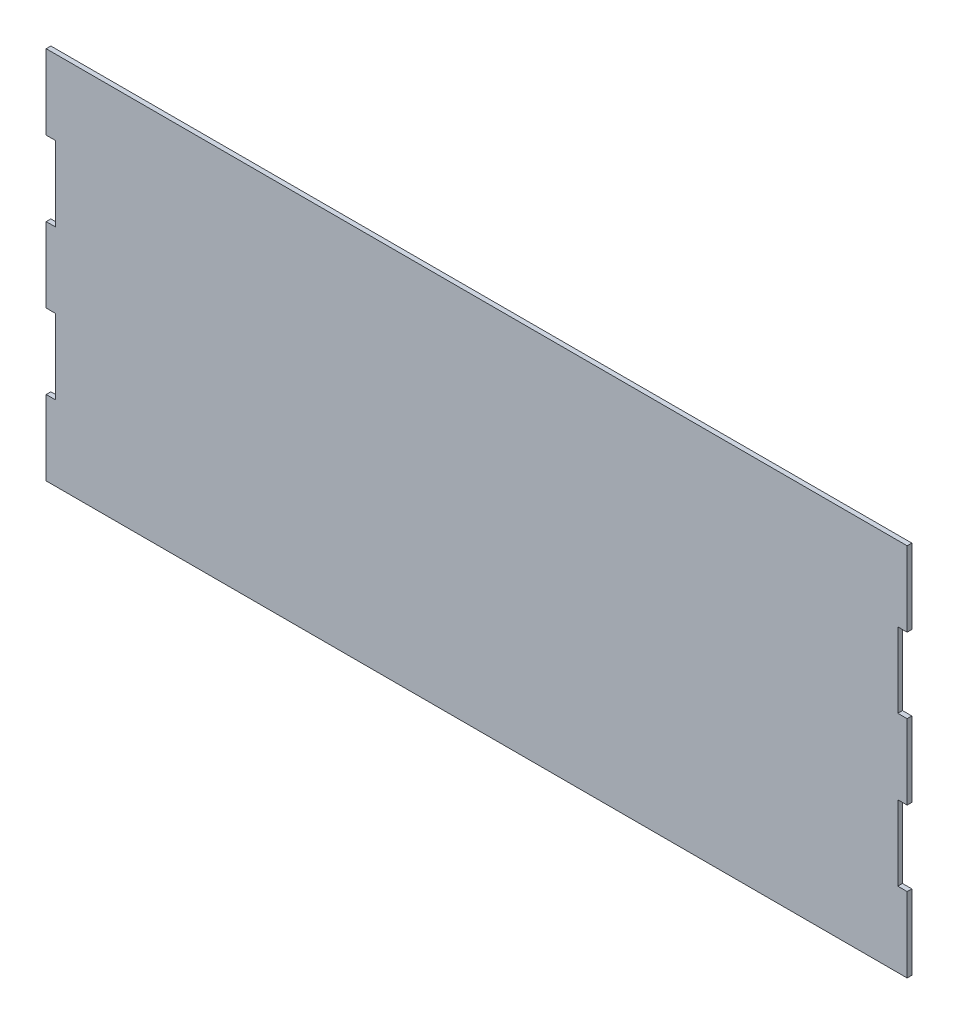
SolidWorks part; units mm, degrees
ref_plane "Front Plane" through (0, 0, 0) normal (0, 0, 1) x (1, 0, 0)
ref_plane "Top Plane" through (0, 0, 0) normal (0, 1, 0) x (1, 0, 0)
ref_plane "Right Plane" through (0, 0, 0) normal (1, 0, 0) x (0, 0, -1)
sketch "Sketch1" plane through (0, 0, 0) normal (0, 0, 1) x (1, 0, 0)
  line L0 (0, 203.2) -> (6.35, 203.2)
  line L1 (0, 0) -> (584.2, 0)
  line L2 (0, 0) -> (0, 50.8)
  line L3 (0, 254) -> (584.2, 254)
  line L4 (584.2, 0) -> (584.2, 50.8)
  line L5 (6.35, 203.2) -> (6.35, 152.4)
  line L6 (6.35, 152.4) -> (0, 152.4)
  line L7 (0, 101.6) -> (6.35, 101.6)
  line L8 (6.35, 101.6) -> (6.35, 50.8)
  line L9 (6.35, 50.8) -> (0, 50.8)
  line L10 (0, 0) -> (6.35, 0)
  line L11 (6.35, 0) -> (6.35, -50.8)
  line L12 (6.35, -50.8) -> (0, -50.8)
  line L13 (0, 101.6) -> (0, 152.4)
  line L14 (0, 203.2) -> (0, 254)
  line L15 (292.1, 254) -> (292.1, 0) construction
  line L16 (577.85, 50.8) -> (584.2, 50.8)
  line L17 (577.85, 101.6) -> (577.85, 50.8)
  line L18 (584.2, 101.6) -> (577.85, 101.6)
  line L19 (577.85, 152.4) -> (584.2, 152.4)
  line L20 (577.85, 203.2) -> (577.85, 152.4)
  line L21 (584.2, 203.2) -> (577.85, 203.2)
  line L22 (584.2, 203.2) -> (584.2, 254)
  line L23 (584.2, 101.6) -> (584.2, 152.4)
  line L24 (25.4, 254) -> (25.4, 0) construction
  line L25 (558.8, 254) -> (558.8, 0) construction
  dimension "D1" = 254
  dimension "D2" = 584.2
  dimension "D3" = 6.35
  dimension "D4" = 50.8
  dimension "D5" = 50.8
  dimension "D7" = 25.4
  dimension "D8" = 25.4
  dimension "D6" = 3
extrude "Boss-Extrude1" add sketch "Sketch1" along normal blind 3.175 contours L18 L23 L19 L20 L21 L22 L3 L14 L0 L5 L6 L13 L7 L8 L9 L2 L1 L4 L16 L17
sketch "Sketch4" plane through (0, 0, 3.175) normal (0, 0, 1) x (1, 0, 0)
  line L1 (312.1555, -0.0167) -> (312.1555, 59.8139)
  line L2 (312.1555, 74.3399) -> (312.1555, 179.5864)
  line L3 (312.1555, 194.1124) -> (312.1555, 254)
  line L4 (308.524, 134.2248) -> (308.524, 239.474)
  line L5 (308.524, 14.4495) -> (308.524, 119.6988)
  line L6 (565.15, 194.1124) -> (565.15, 254)
  line L7 (65.2135, -0.0167) -> (57.9505, -0.0167)
  line L8 (312.1555, -0.0167) -> (319.4185, -0.0167)
  line L9 (312.1555, 254) -> (319.4185, 254)
  line L10 (57.9505, -0.0167) -> (45.8455, -0.0167)
  line L11 (65.2135, 254) -> (57.9505, 254)
  line L12 (57.9505, 254) -> (45.8455, 254)
  line L13 (68.845, 134.2248) -> (68.845, 239.474)
  line L14 (54.319, 134.2248) -> (54.319, 239.474)
  line L15 (61.582, 134.2248) -> (61.582, 239.474)
  line L16 (57.9505, 74.3399) -> (57.9505, 179.5864)
  line L17 (61.582, 14.4495) -> (61.582, 119.6988)
  line L18 (65.2135, 194.1124) -> (65.2135, 254)
  line L19 (70.948, 14.4495) -> (70.948, 119.6988)
  line L20 (57.9505, 194.1124) -> (57.9505, 254)
  line L21 (54.319, 14.4495) -> (54.319, 119.6988)
  line L22 (65.2135, 74.3399) -> (65.2135, 179.5864)
  line L23 (65.2135, -0.0167) -> (65.2135, 59.8139)
  line L24 (57.9505, -0.0167) -> (57.9505, 59.8139)
  line L25 (72.4765, -0.0167) -> (65.2135, -0.0167)
  line L26 (79.7395, 254) -> (72.4765, 254)
  line L27 (72.4765, 254) -> (65.2135, 254)
  line L28 (79.7395, -0.0167) -> (72.4765, -0.0167)
  line L29 (94.2655, 254) -> (87.0025, 254)
  line L30 (87.0025, 254) -> (79.7395, 254)
  line L31 (94.2655, -0.0167) -> (87.0025, -0.0167)
  line L32 (87.0025, -0.0167) -> (79.7395, -0.0167)
  line L33 (76.108, 134.2248) -> (76.108, 239.474)
  line L34 (90.634, 14.4495) -> (90.634, 119.6988)
  line L35 (94.2655, 194.1124) -> (94.2655, 254)
  line L36 (97.897, 134.2248) -> (97.897, 239.474)
  line L37 (72.4765, -0.0167) -> (72.4765, 59.8139)
  line L38 (79.7395, 194.1124) -> (79.7395, 254)
  line L39 (72.4765, 74.3399) -> (72.4765, 179.5864)
  line L40 (90.634, 134.2248) -> (90.634, 239.474)
  line L41 (94.2655, 74.3399) -> (94.2655, 179.5864)
  line L42 (79.7395, 74.3399) -> (79.7395, 179.5864)
  line L43 (87.0025, 74.3399) -> (87.0025, 179.5864)
  line L44 (97.897, 14.4495) -> (97.897, 119.6988)
  line L45 (83.371, 134.2248) -> (83.371, 239.474)
  line L46 (72.4765, 194.1124) -> (72.4765, 254)
  line L47 (76.108, 14.4495) -> (76.108, 119.6988)
  line L48 (79.7395, -0.0167) -> (79.7395, 59.8139)
  line L49 (83.371, 14.4495) -> (83.371, 119.6988)
  line L50 (87.0025, 194.1124) -> (87.0025, 254)
  line L51 (94.2655, -0.0167) -> (94.2655, 59.8139)
  line L52 (87.0025, -0.0167) -> (87.0025, 59.8139)
  line L53 (101.5285, 254) -> (94.2655, 254)
  line L54 (108.7915, -0.0167) -> (101.5285, -0.0167)
  line L55 (101.5285, -0.0167) -> (94.2655, -0.0167)
  line L56 (108.7915, 254) -> (101.5285, 254)
  line L57 (123.3175, -0.0167) -> (116.0545, -0.0167)
  line L58 (116.0545, -0.0167) -> (108.7915, -0.0167)
  line L59 (123.3175, 254) -> (116.0545, 254)
  line L60 (116.0545, 254) -> (108.7915, 254)
  line L61 (119.686, 134.2248) -> (119.686, 239.474)
  line L62 (101.5285, -0.0167) -> (101.5285, 59.8139)
  line L63 (101.5285, 194.1124) -> (101.5285, 254)
  line L64 (108.7915, -0.0167) -> (108.7915, 59.8139)
  line L65 (105.16, 14.4495) -> (105.16, 119.6988)
  line L66 (108.7915, 194.1124) -> (108.7915, 254)
  line L67 (123.3175, 194.1124) -> (123.3175, 254)
  line L68 (101.5285, 74.3399) -> (101.5285, 179.5864)
  line L69 (123.3175, 74.3399) -> (123.3175, 179.5864)
  line L70 (126.949, 14.4495) -> (126.949, 119.6988)
  line L71 (108.7915, 74.3399) -> (108.7915, 179.5864)
  line L72 (126.949, 134.2248) -> (126.949, 239.474)
  line L73 (112.423, 134.2248) -> (112.423, 239.474)
  line L74 (112.423, 14.4495) -> (112.423, 119.6988)
  line L75 (116.0545, 74.3399) -> (116.0545, 179.5864)
  line L76 (116.0545, 194.1124) -> (116.0545, 254)
  line L77 (105.16, 134.2248) -> (105.16, 239.474)
  line L78 (119.686, 14.4495) -> (119.686, 119.6988)
  line L80 (123.3175, -0.0167) -> (123.3175, 59.8139)
  line L81 (116.0545, -0.0167) -> (116.0545, 59.8139)
  line L83 (130.5805, -0.0167) -> (123.3175, -0.0167)
  line L85 (137.8435, -0.0167) -> (130.5805, -0.0167)
  line L86 (137.8435, 254) -> (130.5805, 254)
  line L87 (130.5805, 254) -> (123.3175, 254)
  line L88 (152.3695, -0.0167) -> (145.1065, -0.0167)
  line L89 (145.1065, -0.0167) -> (137.8435, -0.0167)
  line L90 (152.3695, 254) -> (145.1065, 254)
  line L91 (145.1065, 254) -> (137.8435, 254)
  line L92 (156.001, 134.2248) -> (156.001, 239.474)
  line L93 (137.8435, 194.1124) -> (137.8435, 254)
  line L94 (134.212, 134.2248) -> (134.212, 239.474)
  line L95 (130.5805, 194.1124) -> (130.5805, 254)
  line L96 (130.5805, -0.0167) -> (130.5805, 59.8139)
  line L97 (137.8435, 74.3399) -> (137.8435, 179.5864)
  line L98 (130.5805, 74.3399) -> (130.5805, 179.5864)
  line L99 (156.001, 14.4495) -> (156.001, 119.6988)
  line L100 (148.738, 134.2248) -> (148.738, 239.474)
  line L101 (141.475, 134.2248) -> (141.475, 239.474)
  line L102 (152.3695, 74.3399) -> (152.3695, 179.5864)
  line L103 (152.3695, 194.1124) -> (152.3695, 254)
  line L104 (148.738, 14.4495) -> (148.738, 119.6988)
  line L105 (137.8435, -0.0167) -> (137.8435, 59.8139)
  line L106 (145.1065, 74.3399) -> (145.1065, 179.5864)
  line L107 (145.1065, 194.1124) -> (145.1065, 254)
  line L108 (134.212, 14.4495) -> (134.212, 119.6988)
  line L109 (141.475, 14.4495) -> (141.475, 119.6988)
  line L110 (152.3695, -0.0167) -> (152.3695, 59.8139)
  line L111 (145.1065, -0.0167) -> (145.1065, 59.8139)
  line L112 (159.6325, -0.0167) -> (152.3695, -0.0167)
  line L113 (174.1585, 254) -> (166.8955, 254)
  line L114 (166.8955, -0.0167) -> (159.6325, -0.0167)
  line L115 (181.4215, 254) -> (174.1585, 254)
  line L116 (166.8955, 254) -> (159.6325, 254)
  line L117 (159.6325, 254) -> (152.3695, 254)
  line L118 (181.4215, -0.0167) -> (174.1585, -0.0167)
  line L119 (174.1585, -0.0167) -> (166.8955, -0.0167)
  line L120 (163.264, 14.4495) -> (163.264, 119.6988)
  line L121 (166.8955, 74.3399) -> (166.8955, 179.5864)
  line L122 (170.527, 14.4495) -> (170.527, 119.6988)
  line L123 (159.6325, 74.3399) -> (159.6325, 179.5864)
  line L124 (185.053, 134.2248) -> (185.053, 239.474)
  line L125 (174.1585, 194.1124) -> (174.1585, 254)
  line L126 (174.1585, 74.3399) -> (174.1585, 179.5864)
  line L127 (185.053, 14.4495) -> (185.053, 119.6988)
  line L128 (177.79, 134.2248) -> (177.79, 239.474)
  line L129 (170.527, 134.2248) -> (170.527, 239.474)
  line L130 (181.4215, 194.1124) -> (181.4215, 254)
  line L131 (159.6325, -0.0167) -> (159.6325, 59.8139)
  line L132 (166.8955, 194.1124) -> (166.8955, 254)
  line L133 (181.4215, 74.3399) -> (181.4215, 179.5864)
  line L134 (177.79, 14.4495) -> (177.79, 119.6988)
  line L135 (159.6325, 194.1124) -> (159.6325, 254)
  line L136 (163.264, 134.2248) -> (163.264, 239.474)
  line L137 (166.8955, -0.0167) -> (166.8955, 59.8139)
  line L138 (181.4215, -0.0167) -> (181.4215, 59.8139)
  line L139 (174.1585, -0.0167) -> (174.1585, 59.8139)
  line L140 (188.6845, 254) -> (181.4215, 254)
  line L141 (203.2105, 254) -> (195.9475, 254)
  line L142 (195.9475, 254) -> (188.6845, 254)
  line L143 (195.9475, -0.0167) -> (188.6845, -0.0167)
  line L144 (188.6845, -0.0167) -> (181.4215, -0.0167)
  line L145 (210.4735, 254) -> (203.2105, 254)
  line L146 (210.4735, -0.0167) -> (203.2105, -0.0167)
  line L147 (203.2105, -0.0167) -> (195.9475, -0.0167)
  line L148 (195.9475, -0.0167) -> (195.9475, 59.8139)
  line L149 (210.4735, 74.3399) -> (210.4735, 179.5864)
  line L150 (195.9475, 74.3399) -> (195.9475, 179.5864)
  line L151 (203.2105, 194.1124) -> (203.2105, 254)
  line L152 (199.579, 134.2248) -> (199.579, 239.474)
  line L153 (203.2105, 74.3399) -> (203.2105, 179.5864)
  line L154 (192.316, 134.2248) -> (192.316, 239.474)
  line L155 (188.6845, -0.0167) -> (188.6845, 59.8139)
  line L156 (199.579, 14.4495) -> (199.579, 119.6988)
  line L157 (206.842, 14.4495) -> (206.842, 119.6988)
  line L158 (188.6845, 194.1124) -> (188.6845, 254)
  line L159 (214.105, 14.4495) -> (214.105, 119.6988)
  line L160 (195.9475, 194.1124) -> (195.9475, 254)
  line L161 (188.6845, 74.3399) -> (188.6845, 179.5864)
  line L162 (192.316, 14.4495) -> (192.316, 119.6988)
  line L163 (210.4735, 194.1124) -> (210.4735, 254)
  line L164 (214.105, 134.2248) -> (214.105, 239.474)
  line L165 (206.842, 134.2248) -> (206.842, 239.474)
  line L166 (210.4735, -0.0167) -> (210.4735, 59.8139)
  line L167 (203.2105, -0.0167) -> (203.2105, 59.8139)
  line L168 (224.9995, 254) -> (217.7365, 254)
  line L169 (217.7365, 254) -> (210.4735, 254)
  line L170 (224.9995, -0.0167) -> (217.7365, -0.0167)
  line L171 (217.7365, -0.0167) -> (210.4735, -0.0167)
  line L172 (232.2625, 254) -> (224.9995, 254)
  line L173 (239.5255, -0.0167) -> (232.2625, -0.0167)
  line L174 (232.2625, -0.0167) -> (224.9995, -0.0167)
  line L175 (239.5255, 254) -> (232.2625, 254)
  line L176 (224.9995, 194.1124) -> (224.9995, 254)
  line L177 (217.7365, 194.1124) -> (217.7365, 254)
  line L178 (217.7365, 74.3399) -> (217.7365, 179.5864)
  line L179 (228.631, 134.2248) -> (228.631, 239.474)
  line L180 (235.894, 134.2248) -> (235.894, 239.474)
  line L181 (239.5255, 74.3399) -> (239.5255, 179.5864)
  line L182 (224.9995, 74.3399) -> (224.9995, 179.5864)
  line L183 (232.2625, 194.1124) -> (232.2625, 254)
  line L184 (243.157, 134.2248) -> (243.157, 239.474)
  line L185 (224.9995, -0.0167) -> (224.9995, 59.8139)
  line L186 (239.5255, 194.1124) -> (239.5255, 254)
  line L187 (228.631, 14.4495) -> (228.631, 119.6988)
  line L188 (221.368, 134.2248) -> (221.368, 239.474)
  line L189 (235.894, 14.4495) -> (235.894, 119.6988)
  line L190 (243.157, 14.4495) -> (243.157, 119.6988)
  line L191 (232.2625, 74.3399) -> (232.2625, 179.5864)
  line L192 (217.7365, -0.0167) -> (217.7365, 59.8139)
  line L193 (221.368, 14.4495) -> (221.368, 119.6988)
  line L194 (239.5255, -0.0167) -> (239.5255, 59.8139)
  line L195 (232.2625, -0.0167) -> (232.2625, 59.8139)
  line L196 (261.3145, 254) -> (254.0515, 254)
  line L197 (254.0515, -0.0167) -> (246.7885, -0.0167)
  line L198 (246.7885, -0.0167) -> (239.5255, -0.0167)
  line L199 (268.5775, 254) -> (261.3145, 254)
  line L200 (254.0515, 254) -> (246.7885, 254)
  line L201 (246.7885, 254) -> (239.5255, 254)
  line L202 (268.5775, -0.0167) -> (261.3145, -0.0167)
  line L203 (261.3145, -0.0167) -> (254.0515, -0.0167)
  line L204 (264.946, 134.2248) -> (264.946, 239.474)
  line L205 (272.209, 134.2248) -> (272.209, 239.474)
  line L206 (261.3145, 194.1124) -> (261.3145, 254)
  line L207 (250.42, 134.2248) -> (250.42, 239.474)
  line L208 (254.0515, 74.3399) -> (254.0515, 179.5864)
  line L209 (257.683, 134.2248) -> (257.683, 239.474)
  line L210 (268.5775, 74.3399) -> (268.5775, 179.5864)
  line L211 (272.209, 14.4495) -> (272.209, 119.6988)
  line L212 (268.5775, 194.1124) -> (268.5775, 254)
  line L213 (257.683, 14.4495) -> (257.683, 119.6988)
  line L214 (254.0515, 194.1124) -> (254.0515, 254)
  line L215 (250.42, 14.4495) -> (250.42, 119.6988)
  line L216 (254.0515, -0.0167) -> (254.0515, 59.8139)
  line L217 (246.7885, -0.0167) -> (246.7885, 59.8139)
  line L218 (264.946, 14.4495) -> (264.946, 119.6988)
  line L219 (261.3145, 74.3399) -> (261.3145, 179.5864)
  line L220 (246.7885, 74.3399) -> (246.7885, 179.5864)
  line L221 (246.7885, 194.1124) -> (246.7885, 254)
  line L222 (268.5775, -0.0167) -> (268.5775, 59.8139)
  line L223 (261.3145, -0.0167) -> (261.3145, 59.8139)
  line L224 (275.8405, 254) -> (268.5775, 254)
  line L225 (275.8405, -0.0167) -> (268.5775, -0.0167)
  line L226 (279.472, 14.4495) -> (279.472, 119.6988)
  line L227 (275.8405, 74.3399) -> (275.8405, 179.5864)
  line L228 (275.8405, -0.0167) -> (275.8405, 59.8139)
  line L229 (275.8405, 194.1124) -> (275.8405, 254)
  line L230 (279.472, 134.2248) -> (279.472, 239.474)
  line L231 (283.1035, 254) -> (275.8405, 254)
  line L232 (283.1035, -0.0167) -> (275.8405, -0.0167)
  line L233 (283.1035, -0.0167) -> (283.1035, 59.8139)
  line L234 (283.1035, 194.1124) -> (283.1035, 254)
  line L235 (286.735, 14.4495) -> (286.735, 119.6988)
  line L236 (283.1035, 74.3399) -> (283.1035, 179.5864)
  line L237 (286.735, 134.2248) -> (286.735, 239.474)
  line L238 (290.3665, 254) -> (283.1035, 254)
  line L239 (290.3665, -0.0167) -> (283.1035, -0.0167)
  line L240 (293.998, 14.4495) -> (293.998, 119.6988)
  line L241 (290.3665, 74.3399) -> (290.3665, 179.5864)
  line L242 (293.998, 134.2248) -> (293.998, 239.474)
  line L243 (290.3665, 194.1124) -> (290.3665, 254)
  line L244 (290.3665, -0.0167) -> (290.3665, 59.8139)
  line L245 (297.6295, 254) -> (290.3665, 254)
  line L246 (297.6295, -0.0167) -> (290.3665, -0.0167)
  line L247 (301.261, 14.4495) -> (301.261, 119.6988)
  line L248 (301.261, 134.2248) -> (301.261, 239.474)
  line L249 (297.6295, 194.1124) -> (297.6295, 254)
  line L250 (297.6295, 74.3399) -> (297.6295, 179.5864)
  line L251 (297.6295, -0.0167) -> (297.6295, 59.8139)
  line L252 (51.898, -0.0167) -> (51.898, 59.8139)
  line L253 (51.898, 74.3399) -> (51.898, 179.5864)
  line L254 (304.8925, 254) -> (297.6295, 254)
  line L255 (304.8925, -0.0167) -> (297.6295, -0.0167)
  line L256 (51.898, 194.1124) -> (51.898, 254)
  line L257 (304.8925, 194.1124) -> (304.8925, 254)
  line L258 (304.8925, 74.3399) -> (304.8925, 179.5864)
  line L259 (304.8925, -0.0167) -> (304.8925, 59.8139)
  line L263 (24.0565, 254) -> (31.3195, 254)
  line L264 (24.0565, -0.0167) -> (31.3195, -0.0167)
  line L268 (20.425, 14.4495) -> (20.425, 119.6988)
  line L269 (24.0565, -0.0167) -> (24.0565, 59.8139)
  line L270 (20.425, 134.2248) -> (20.425, 239.474)
  line L273 (24.0565, 74.3399) -> (24.0565, 179.5864)
  line L276 (24.0565, 194.1124) -> (24.0565, 254)
  line L280 (16.7935, -0.0167) -> (24.0565, -0.0167)
  line L282 (16.7935, 254) -> (24.0565, 254)
  line L284 (27.688, 14.4495) -> (27.688, 119.6988)
  line L285 (31.3195, 194.1124) -> (31.3195, 254)
  line L286 (31.3195, 74.3399) -> (31.3195, 179.5864)
  line L287 (31.3195, -0.0167) -> (31.3195, 59.8139)
  line L288 (27.688, 134.2248) -> (27.688, 239.474)
  line L289 (31.3195, 254) -> (38.5825, 254)
  line L290 (31.3195, -0.0167) -> (38.5825, -0.0167)
  line L291 (45.8455, -0.0167) -> (45.8455, 59.8139)
  line L292 (38.5825, -0.0167) -> (38.5825, 59.8139)
  line L293 (38.5825, 74.3399) -> (38.5825, 179.5864)
  line L294 (49.477, 14.4495) -> (49.477, 119.6988)
  line L295 (45.8455, 194.1124) -> (45.8455, 254)
  line L296 (32.848, 14.4495) -> (32.848, 119.6988)
  line L297 (38.5825, 194.1124) -> (38.5825, 254)
  line L298 (42.214, 14.4495) -> (42.214, 119.6988)
  line L299 (45.8455, 74.3399) -> (45.8455, 179.5864)
  line L300 (42.214, 134.2248) -> (42.214, 239.474)
  line L301 (49.477, 134.2248) -> (49.477, 239.474)
  line L302 (34.951, 134.2248) -> (34.951, 239.474)
  line L303 (38.5825, 254) -> (45.8455, 254)
  line L304 (38.5825, -0.0167) -> (45.8455, -0.0167)
  line L541 (565.15, 74.3399) -> (565.15, 179.5864)
  line L542 (565.15, -0.0167) -> (565.15, 59.8139)
  line L543 (319.4185, -0.0167) -> (319.4185, 59.8139)
  line L544 (319.4185, 74.3399) -> (319.4185, 179.5864)
  line L545 (319.4185, 194.1124) -> (319.4185, 254)
  line L546 (315.787, 134.2248) -> (315.787, 239.474)
  line L547 (315.787, 14.4495) -> (315.787, 119.6988)
  line L548 (319.4185, -0.0167) -> (326.6815, -0.0167)
  line L549 (319.4185, 254) -> (326.6815, 254)
  line L550 (326.6815, -0.0167) -> (326.6815, 59.8139)
  line L551 (326.6815, 194.1124) -> (326.6815, 254)
  line L552 (323.05, 134.2248) -> (323.05, 239.474)
  line L553 (326.6815, 74.3399) -> (326.6815, 179.5864)
  line L554 (323.05, 14.4495) -> (323.05, 119.6988)
  line L555 (326.6815, -0.0167) -> (333.9445, -0.0167)
  line L556 (326.6815, 254) -> (333.9445, 254)
  line L557 (330.313, 134.2248) -> (330.313, 239.474)
  line L558 (333.9445, 74.3399) -> (333.9445, 179.5864)
  line L559 (330.313, 14.4495) -> (330.313, 119.6988)
  line L560 (333.9445, 194.1124) -> (333.9445, 254)
  line L561 (333.9445, -0.0167) -> (333.9445, 59.8139)
  line L562 (333.9445, -0.0167) -> (341.2075, -0.0167)
  line L563 (333.9445, 254) -> (341.2075, 254)
  line L564 (337.576, 134.2248) -> (337.576, 239.474)
  line L565 (341.2075, 194.1124) -> (341.2075, 254)
  line L566 (341.2075, -0.0167) -> (341.2075, 59.8139)
  line L567 (341.2075, 74.3399) -> (341.2075, 179.5864)
  line L568 (337.576, 14.4495) -> (337.576, 119.6988)
  line L569 (341.2075, -0.0167) -> (348.4705, -0.0167)
  line L570 (341.2075, 254) -> (348.4705, 254)
  line L571 (355.7335, -0.0167) -> (355.7335, 59.8139)
  line L572 (348.4705, -0.0167) -> (348.4705, 59.8139)
  line L573 (370.2595, 194.1124) -> (370.2595, 254)
  line L574 (370.2595, 74.3399) -> (370.2595, 179.5864)
  line L575 (355.7335, 74.3399) -> (355.7335, 179.5864)
  line L576 (352.102, 14.4495) -> (352.102, 119.6988)
  line L577 (370.2595, -0.0167) -> (370.2595, 59.8139)
  line L578 (362.9965, -0.0167) -> (362.9965, 59.8139)
  line L579 (366.628, 14.4495) -> (366.628, 119.6988)
  line L580 (362.9965, 194.1124) -> (362.9965, 254)
  line L581 (359.365, 14.4495) -> (359.365, 119.6988)
  line L582 (348.4705, 194.1124) -> (348.4705, 254)
  line L583 (344.839, 14.4495) -> (344.839, 119.6988)
  line L584 (348.4705, 74.3399) -> (348.4705, 179.5864)
  line L585 (359.365, 134.2248) -> (359.365, 239.474)
  line L586 (362.9965, 74.3399) -> (362.9965, 179.5864)
  line L587 (366.628, 134.2248) -> (366.628, 239.474)
  line L588 (355.7335, 194.1124) -> (355.7335, 254)
  line L589 (344.839, 134.2248) -> (344.839, 239.474)
  line L590 (352.102, 134.2248) -> (352.102, 239.474)
  line L591 (355.7335, -0.0167) -> (362.9965, -0.0167)
  line L592 (348.4705, -0.0167) -> (355.7335, -0.0167)
  line L593 (370.2595, 254) -> (377.5225, 254)
  line L594 (362.9965, 254) -> (370.2595, 254)
  line L595 (348.4705, 254) -> (355.7335, 254)
  line L596 (370.2595, -0.0167) -> (377.5225, -0.0167)
  line L597 (362.9965, -0.0167) -> (370.2595, -0.0167)
  line L598 (355.7335, 254) -> (362.9965, 254)
  line L599 (384.7855, -0.0167) -> (384.7855, 59.8139)
  line L600 (377.5225, -0.0167) -> (377.5225, 59.8139)
  line L601 (395.68, 14.4495) -> (395.68, 119.6988)
  line L602 (399.3115, -0.0167) -> (399.3115, 59.8139)
  line L603 (384.7855, 74.3399) -> (384.7855, 179.5864)
  line L604 (373.891, 14.4495) -> (373.891, 119.6988)
  line L605 (381.154, 14.4495) -> (381.154, 119.6988)
  line L606 (395.68, 134.2248) -> (395.68, 239.474)
  line L607 (388.417, 14.4495) -> (388.417, 119.6988)
  line L608 (377.5225, 194.1124) -> (377.5225, 254)
  line L609 (392.0485, -0.0167) -> (392.0485, 59.8139)
  line L610 (373.891, 134.2248) -> (373.891, 239.474)
  line L611 (384.7855, 194.1124) -> (384.7855, 254)
  line L612 (392.0485, 74.3399) -> (392.0485, 179.5864)
  line L613 (377.5225, 74.3399) -> (377.5225, 179.5864)
  line L614 (381.154, 134.2248) -> (381.154, 239.474)
  line L615 (388.417, 134.2248) -> (388.417, 239.474)
  line L616 (399.3115, 74.3399) -> (399.3115, 179.5864)
  line L617 (399.3115, 194.1124) -> (399.3115, 254)
  line L618 (392.0485, 194.1124) -> (392.0485, 254)
  line L619 (377.5225, 254) -> (384.7855, 254)
  line L620 (384.7855, -0.0167) -> (392.0485, -0.0167)
  line L621 (377.5225, -0.0167) -> (384.7855, -0.0167)
  line L622 (384.7855, 254) -> (392.0485, 254)
  line L623 (399.3115, -0.0167) -> (406.5745, -0.0167)
  line L624 (392.0485, -0.0167) -> (399.3115, -0.0167)
  line L625 (399.3115, 254) -> (406.5745, 254)
  line L626 (392.0485, 254) -> (399.3115, 254)
  line L627 (413.8375, -0.0167) -> (413.8375, 59.8139)
  line L628 (406.5745, -0.0167) -> (406.5745, 59.8139)
  line L629 (410.206, 134.2248) -> (410.206, 239.474)
  line L630 (402.943, 134.2248) -> (402.943, 239.474)
  line L631 (406.5745, 194.1124) -> (406.5745, 254)
  line L632 (424.732, 14.4495) -> (424.732, 119.6988)
  line L633 (428.3635, 74.3399) -> (428.3635, 179.5864)
  line L634 (421.1005, 194.1124) -> (421.1005, 254)
  line L635 (402.943, 14.4495) -> (402.943, 119.6988)
  line L636 (428.3635, 194.1124) -> (428.3635, 254)
  line L637 (410.206, 14.4495) -> (410.206, 119.6988)
  line L638 (417.469, 14.4495) -> (417.469, 119.6988)
  line L639 (428.3635, -0.0167) -> (428.3635, 59.8139)
  line L640 (424.732, 134.2248) -> (424.732, 239.474)
  line L641 (413.8375, 74.3399) -> (413.8375, 179.5864)
  line L642 (417.469, 134.2248) -> (417.469, 239.474)
  line L643 (413.8375, 194.1124) -> (413.8375, 254)
  line L644 (421.1005, 74.3399) -> (421.1005, 179.5864)
  line L645 (406.5745, 74.3399) -> (406.5745, 179.5864)
  line L646 (421.1005, -0.0167) -> (421.1005, 59.8139)
  line L647 (413.8375, -0.0167) -> (421.1005, -0.0167)
  line L648 (406.5745, -0.0167) -> (413.8375, -0.0167)
  line L649 (406.5745, 254) -> (413.8375, 254)
  line L650 (428.3635, -0.0167) -> (435.6265, -0.0167)
  line L651 (421.1005, -0.0167) -> (428.3635, -0.0167)
  line L652 (421.1005, 254) -> (428.3635, 254)
  line L653 (413.8375, 254) -> (421.1005, 254)
  line L654 (428.3635, 254) -> (435.6265, 254)
  line L655 (442.8895, -0.0167) -> (442.8895, 59.8139)
  line L656 (435.6265, -0.0167) -> (435.6265, 59.8139)
  line L657 (450.1525, -0.0167) -> (450.1525, 59.8139)
  line L658 (453.784, 134.2248) -> (453.784, 239.474)
  line L659 (457.4155, 194.1124) -> (457.4155, 254)
  line L660 (439.258, 14.4495) -> (439.258, 119.6988)
  line L661 (435.6265, 74.3399) -> (435.6265, 179.5864)
  line L662 (450.1525, 194.1124) -> (450.1525, 254)
  line L663 (457.4155, -0.0167) -> (457.4155, 59.8139)
  line L664 (435.6265, 194.1124) -> (435.6265, 254)
  line L665 (446.521, 134.2248) -> (446.521, 239.474)
  line L666 (439.258, 134.2248) -> (439.258, 239.474)
  line L667 (431.995, 14.4495) -> (431.995, 119.6988)
  line L668 (442.8895, 74.3399) -> (442.8895, 179.5864)
  line L669 (442.8895, 194.1124) -> (442.8895, 254)
  line L670 (431.995, 134.2248) -> (431.995, 239.474)
  line L671 (457.4155, 74.3399) -> (457.4155, 179.5864)
  line L672 (446.521, 14.4495) -> (446.521, 119.6988)
  line L673 (450.1525, 74.3399) -> (450.1525, 179.5864)
  line L674 (453.784, 14.4495) -> (453.784, 119.6988)
  line L675 (442.8895, -0.0167) -> (450.1525, -0.0167)
  line L676 (435.6265, -0.0167) -> (442.8895, -0.0167)
  line L677 (457.4155, 254) -> (464.6785, 254)
  line L678 (450.1525, 254) -> (457.4155, 254)
  line L679 (435.6265, 254) -> (442.8895, 254)
  line L680 (450.1525, -0.0167) -> (457.4155, -0.0167)
  line L681 (442.8895, 254) -> (450.1525, 254)
  line L682 (457.4155, -0.0167) -> (464.6785, -0.0167)
  line L683 (471.9415, -0.0167) -> (471.9415, 59.8139)
  line L684 (464.6785, -0.0167) -> (464.6785, 59.8139)
  line L685 (475.573, 14.4495) -> (475.573, 119.6988)
  line L686 (482.836, 14.4495) -> (482.836, 119.6988)
  line L687 (471.9415, 194.1124) -> (471.9415, 254)
  line L688 (471.9415, 74.3399) -> (471.9415, 179.5864)
  line L689 (479.2045, -0.0167) -> (479.2045, 59.8139)
  line L690 (468.31, 14.4495) -> (468.31, 119.6988)
  line L691 (464.6785, 194.1124) -> (464.6785, 254)
  line L692 (464.6785, 74.3399) -> (464.6785, 179.5864)
  line L693 (475.573, 134.2248) -> (475.573, 239.474)
  line L694 (468.31, 134.2248) -> (468.31, 239.474)
  line L695 (461.047, 14.4495) -> (461.047, 119.6988)
  line L696 (486.4675, 74.3399) -> (486.4675, 179.5864)
  line L697 (479.2045, 74.3399) -> (479.2045, 179.5864)
  line L698 (486.4675, -0.0167) -> (486.4675, 59.8139)
  line L699 (486.4675, 194.1124) -> (486.4675, 254)
  line L700 (482.836, 134.2248) -> (482.836, 239.474)
  line L701 (479.2045, 194.1124) -> (479.2045, 254)
  line L702 (461.047, 134.2248) -> (461.047, 239.474)
  line L703 (471.9415, 254) -> (479.2045, 254)
  line L704 (464.6785, 254) -> (471.9415, 254)
  line L705 (471.9415, -0.0167) -> (479.2045, -0.0167)
  line L706 (464.6785, -0.0167) -> (471.9415, -0.0167)
  line L707 (486.4675, 254) -> (493.7305, 254)
  line L708 (479.2045, 254) -> (486.4675, 254)
  line L709 (479.2045, -0.0167) -> (486.4675, -0.0167)
  line L710 (486.4675, -0.0167) -> (493.7305, -0.0167)
  line L711 (500.9935, -0.0167) -> (500.9935, 59.8139)
  line L712 (493.7305, -0.0167) -> (493.7305, 59.8139)
  line L713 (497.362, 14.4495) -> (497.362, 119.6988)
  line L714 (511.888, 134.2248) -> (511.888, 239.474)
  line L715 (500.9935, 194.1124) -> (500.9935, 254)
  line L716 (500.9935, 74.3399) -> (500.9935, 179.5864)
  line L717 (504.625, 14.4495) -> (504.625, 119.6988)
  line L718 (504.625, 134.2248) -> (504.625, 239.474)
  line L719 (490.099, 134.2248) -> (490.099, 239.474)
  line L720 (508.2565, 74.3399) -> (508.2565, 179.5864)
  line L721 (490.099, 14.4495) -> (490.099, 119.6988)
  line L722 (493.7305, 74.3399) -> (493.7305, 179.5864)
  line L723 (515.5195, 74.3399) -> (515.5195, 179.5864)
  line L724 (493.7305, 194.1124) -> (493.7305, 254)
  line L725 (508.2565, 194.1124) -> (508.2565, 254)
  line L726 (511.888, 14.4495) -> (511.888, 119.6988)
  line L727 (508.2565, -0.0167) -> (508.2565, 59.8139)
  line L728 (515.5195, 194.1124) -> (515.5195, 254)
  line L729 (515.5195, -0.0167) -> (515.5195, 59.8139)
  line L730 (497.362, 134.2248) -> (497.362, 239.474)
  line L731 (500.9935, 254) -> (508.2565, 254)
  line L732 (493.7305, 254) -> (500.9935, 254)
  line L733 (500.9935, -0.0167) -> (508.2565, -0.0167)
  line L734 (493.7305, -0.0167) -> (500.9935, -0.0167)
  line L735 (508.2565, 254) -> (515.5195, 254)
  line L736 (515.5195, -0.0167) -> (522.7825, -0.0167)
  line L737 (508.2565, -0.0167) -> (515.5195, -0.0167)
  line L738 (515.5195, 254) -> (522.7825, 254)
  line L739 (530.0455, -0.0167) -> (530.0455, 59.8139)
  line L740 (522.7825, -0.0167) -> (522.7825, 59.8139)
  line L741 (530.0455, 194.1124) -> (530.0455, 254)
  line L742 (533.677, 14.4495) -> (533.677, 119.6988)
  line L743 (537.3085, -0.0167) -> (537.3085, 59.8139)
  line L744 (540.94, 14.4495) -> (540.94, 119.6988)
  line L745 (544.5715, 194.1124) -> (544.5715, 254)
  line L746 (533.677, 134.2248) -> (533.677, 239.474)
  line L747 (519.151, 14.4495) -> (519.151, 119.6988)
  line L748 (530.0455, 74.3399) -> (530.0455, 179.5864)
  line L749 (537.3085, 74.3399) -> (537.3085, 179.5864)
  line L750 (522.7825, 74.3399) -> (522.7825, 179.5864)
  line L751 (526.414, 134.2248) -> (526.414, 239.474)
  line L752 (544.5715, 74.3399) -> (544.5715, 179.5864)
  line L753 (537.3085, 194.1124) -> (537.3085, 254)
  line L754 (544.5715, -0.0167) -> (544.5715, 59.8139)
  line L755 (519.151, 134.2248) -> (519.151, 239.474)
  line L756 (522.7825, 194.1124) -> (522.7825, 254)
  line L757 (526.414, 14.4495) -> (526.414, 119.6988)
  line L758 (540.94, 134.2248) -> (540.94, 239.474)
  line L759 (530.0455, -0.0167) -> (537.3085, -0.0167)
  line L760 (522.7825, -0.0167) -> (530.0455, -0.0167)
  line L761 (530.0455, 254) -> (537.3085, 254)
  line L762 (522.7825, 254) -> (530.0455, 254)
  line L763 (537.3085, -0.0167) -> (544.5715, -0.0167)
  line L764 (544.5715, 254) -> (551.8345, 254)
  line L765 (537.3085, 254) -> (544.5715, 254)
  line L766 (544.5715, -0.0167) -> (551.8345, -0.0167)
  line L767 (559.0975, -0.0167) -> (559.0975, 59.8139)
  line L768 (551.8345, -0.0167) -> (551.8345, 59.8139)
  line L769 (551.8345, 74.3399) -> (551.8345, 179.5864)
  line L770 (562.729, 14.4495) -> (562.729, 119.6988)
  line L771 (559.0975, 194.1124) -> (559.0975, 254)
  line L772 (546.1, 14.4495) -> (546.1, 119.6988)
  line L773 (551.8345, 194.1124) -> (551.8345, 254)
  line L774 (555.466, 14.4495) -> (555.466, 119.6988)
  line L775 (559.0975, 74.3399) -> (559.0975, 179.5864)
  line L776 (555.466, 134.2248) -> (555.466, 239.474)
  line L777 (562.729, 134.2248) -> (562.729, 239.474)
  line L778 (548.203, 134.2248) -> (548.203, 239.474)
  line L779 (559.0975, 254) -> (565.15, 254)
  line L780 (551.8345, 254) -> (559.0975, 254)
  line L781 (559.0975, -0.0167) -> (565.15, -0.0167)
  line L782 (551.8345, -0.0167) -> (559.0975, -0.0167)
  point P0 (0, 0)
  point P3 (0, 0)
  point P4 (0, 0)
  point P378 (0, 0)
  point P379 (0, 0)
sketch "Sketch5" plane through (0, 0, 3.175) normal (0, 0, 1) x (1, 0, 0)
  line L0 (565.15, 319.4437) -> (565.15, -63.9302) construction
  line L1 (558.8, -29.6999) -> (558.8, 49970.3001) construction
  line L3 (308.524, -52.4876) -> (308.524, -50052.4876) construction
  line L5 (51.898, -55.1089) -> (51.898, 49944.8911) construction
  line L7 (19.05, 13.735) -> (19.05, -49986.265) construction
